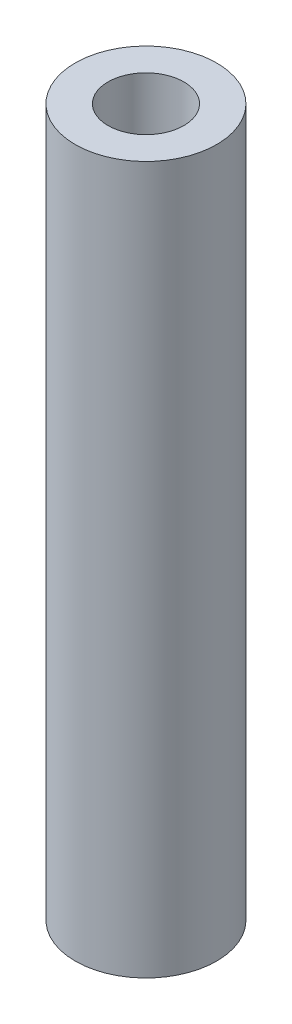
SolidWorks part; units mm, degrees
ref_plane "Front Plane" through (0, 0, 0) normal (0, 0, 1) x (1, 0, 0)
ref_plane "Top Plane" through (0, 0, 0) normal (0, 1, 0) x (1, 0, 0)
ref_plane "Right Plane" through (0, 0, 0) normal (1, 0, 0) x (0, 0, -1)
sketch "Sketch1" plane through (0, 0, 0) normal (0, 1, 0) x (1, 0, 0)
  circle A0 centre (0, 0) radius 3.175
  circle A1 centre (0, 0) radius 1.7018
  dimension "D1" = 3.4036
  dimension "D2" = 6.35
extrude "Extrude1" add sketch "Sketch1" along normal blind 31.75
